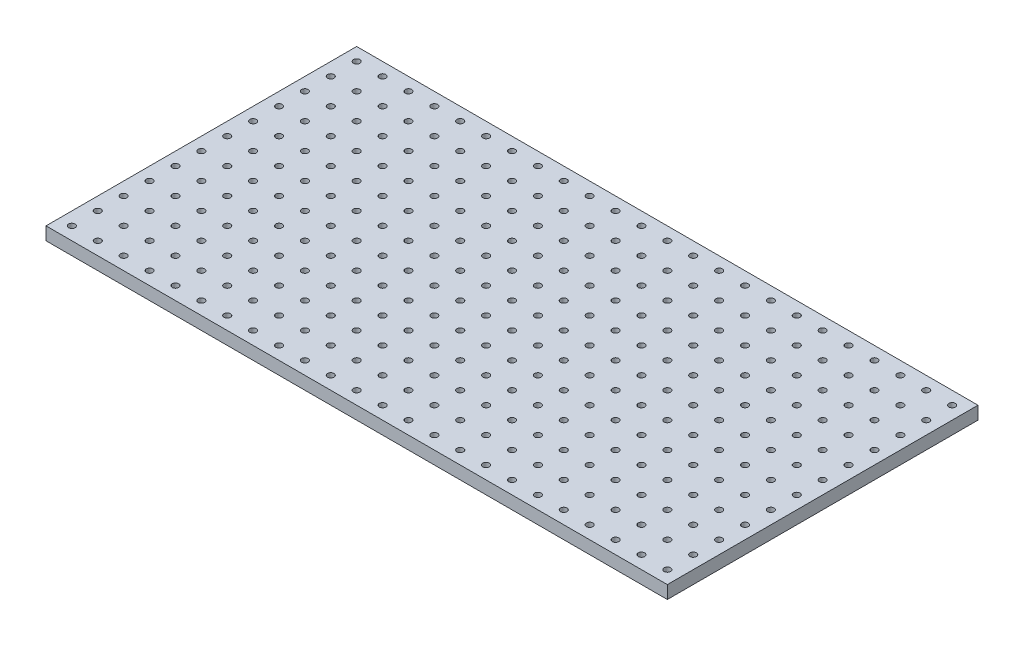
SolidWorks part; units mm, degrees
ref_plane "Front Plane" through (0, 0, 0) normal (0, 0, 1) x (1, 0, 0)
ref_plane "Top Plane" through (0, 0, 0) normal (0, 1, 0) x (1, 0, 0)
ref_plane "Right Plane" through (0, 0, 0) normal (1, 0, 0) x (0, 0, -1)
sketch "Sketch1" plane through (0, 0, 0) normal (0, 1, 0) x (1, 0, 0)
  line L1 (0, 0) -> (609.6, 0)
  line L2 (0, 0) -> (0, 304.8)
  line L3 (0, 304.8) -> (609.6, 304.8)
  line L4 (609.6, 0) -> (609.6, 304.8)
  dimension "D1" = 304.8
  dimension "D2" = 609.6
extrude "Boss-Extrude1" add sketch "Sketch1" along normal blind 12.7
sketch "Sketch2" plane through (0, 12.7, 0) normal (0, 1, 0) x (1, 0, 0)
  line L0 (0, 0) -> (609.6, 0) construction
  line L1 (0, 304.8) -> (0, 0) construction
  circle A0 centre (12.7, 12.7) radius 3.175
  circle A1 centre (38.1, 12.7) radius 3.175
  circle A2 centre (63.5, 12.7) radius 3.175
  circle A3 centre (88.9, 12.7) radius 3.175
  circle A4 centre (114.3, 12.7) radius 3.175
  circle A5 centre (139.7, 12.7) radius 3.175
  circle A6 centre (165.1, 12.7) radius 3.175
  circle A7 centre (190.5, 12.7) radius 3.175
  circle A8 centre (215.9, 12.7) radius 3.175
  circle A9 centre (241.3, 12.7) radius 3.175
  circle A10 centre (266.7, 12.7) radius 3.175
  circle A11 centre (292.1, 12.7) radius 3.175
  circle A12 centre (317.5, 12.7) radius 3.175
  circle A13 centre (342.9, 12.7) radius 3.175
  circle A14 centre (368.3, 12.7) radius 3.175
  circle A15 centre (393.7, 12.7) radius 3.175
  circle A16 centre (419.1, 12.7) radius 3.175
  circle A17 centre (444.5, 12.7) radius 3.175
  circle A18 centre (469.9, 12.7) radius 3.175
  circle A19 centre (495.3, 12.7) radius 3.175
  circle A20 centre (520.7, 12.7) radius 3.175
  circle A21 centre (546.1, 12.7) radius 3.175
  circle A22 centre (571.5, 12.7) radius 3.175
  circle A23 centre (596.9, 12.7) radius 3.175
  circle A24 centre (38.1, 38.1) radius 3.175
  circle A25 centre (63.5, 38.1) radius 3.175
  circle A26 centre (88.9, 38.1) radius 3.175
  circle A27 centre (114.3, 38.1) radius 3.175
  circle A28 centre (139.7, 38.1) radius 3.175
  circle A29 centre (165.1, 38.1) radius 3.175
  circle A30 centre (190.5, 38.1) radius 3.175
  circle A31 centre (215.9, 38.1) radius 3.175
  circle A32 centre (241.3, 38.1) radius 3.175
  circle A33 centre (266.7, 38.1) radius 3.175
  circle A34 centre (292.1, 38.1) radius 3.175
  circle A35 centre (317.5, 38.1) radius 3.175
  circle A36 centre (342.9, 38.1) radius 3.175
  circle A37 centre (368.3, 38.1) radius 3.175
  circle A38 centre (393.7, 38.1) radius 3.175
  circle A39 centre (419.1, 38.1) radius 3.175
  circle A40 centre (444.5, 38.1) radius 3.175
  circle A41 centre (469.9, 38.1) radius 3.175
  circle A42 centre (495.3, 38.1) radius 3.175
  circle A43 centre (520.7, 38.1) radius 3.175
  circle A44 centre (546.1, 38.1) radius 3.175
  circle A45 centre (571.5, 38.1) radius 3.175
  circle A46 centre (596.9, 38.1) radius 3.175
  circle A47 centre (38.1, 63.5) radius 3.175
  circle A48 centre (63.5, 63.5) radius 3.175
  circle A49 centre (88.9, 63.5) radius 3.175
  circle A50 centre (114.3, 63.5) radius 3.175
  circle A51 centre (139.7, 63.5) radius 3.175
  circle A52 centre (165.1, 63.5) radius 3.175
  circle A53 centre (190.5, 63.5) radius 3.175
  circle A54 centre (215.9, 63.5) radius 3.175
  circle A55 centre (241.3, 63.5) radius 3.175
  circle A56 centre (266.7, 63.5) radius 3.175
  circle A57 centre (292.1, 63.5) radius 3.175
  circle A58 centre (317.5, 63.5) radius 3.175
  circle A59 centre (342.9, 63.5) radius 3.175
  circle A60 centre (368.3, 63.5) radius 3.175
  circle A61 centre (393.7, 63.5) radius 3.175
  circle A62 centre (419.1, 63.5) radius 3.175
  circle A63 centre (444.5, 63.5) radius 3.175
  circle A64 centre (469.9, 63.5) radius 3.175
  circle A65 centre (495.3, 63.5) radius 3.175
  circle A66 centre (520.7, 63.5) radius 3.175
  circle A67 centre (546.1, 63.5) radius 3.175
  circle A68 centre (571.5, 63.5) radius 3.175
  circle A69 centre (596.9, 63.5) radius 3.175
  circle A70 centre (38.1, 88.9) radius 3.175
  circle A71 centre (63.5, 88.9) radius 3.175
  circle A72 centre (88.9, 88.9) radius 3.175
  circle A73 centre (114.3, 88.9) radius 3.175
  circle A74 centre (139.7, 88.9) radius 3.175
  circle A75 centre (165.1, 88.9) radius 3.175
  circle A76 centre (190.5, 88.9) radius 3.175
  circle A77 centre (215.9, 88.9) radius 3.175
  circle A78 centre (241.3, 88.9) radius 3.175
  circle A79 centre (266.7, 88.9) radius 3.175
  circle A80 centre (292.1, 88.9) radius 3.175
  circle A81 centre (317.5, 88.9) radius 3.175
  circle A82 centre (342.9, 88.9) radius 3.175
  circle A83 centre (368.3, 88.9) radius 3.175
  circle A84 centre (393.7, 88.9) radius 3.175
  circle A85 centre (419.1, 88.9) radius 3.175
  circle A86 centre (444.5, 88.9) radius 3.175
  circle A87 centre (469.9, 88.9) radius 3.175
  circle A88 centre (495.3, 88.9) radius 3.175
  circle A89 centre (520.7, 88.9) radius 3.175
  circle A90 centre (546.1, 88.9) radius 3.175
  circle A91 centre (571.5, 88.9) radius 3.175
  circle A92 centre (596.9, 88.9) radius 3.175
  circle A93 centre (38.1, 114.3) radius 3.175
  circle A94 centre (63.5, 114.3) radius 3.175
  circle A95 centre (88.9, 114.3) radius 3.175
  circle A96 centre (114.3, 114.3) radius 3.175
  circle A97 centre (139.7, 114.3) radius 3.175
  circle A98 centre (165.1, 114.3) radius 3.175
  circle A99 centre (190.5, 114.3) radius 3.175
  circle A100 centre (215.9, 114.3) radius 3.175
  circle A101 centre (241.3, 114.3) radius 3.175
  circle A102 centre (266.7, 114.3) radius 3.175
  circle A103 centre (292.1, 114.3) radius 3.175
  circle A104 centre (317.5, 114.3) radius 3.175
  circle A105 centre (342.9, 114.3) radius 3.175
  circle A106 centre (368.3, 114.3) radius 3.175
  circle A107 centre (393.7, 114.3) radius 3.175
  circle A108 centre (419.1, 114.3) radius 3.175
  circle A109 centre (444.5, 114.3) radius 3.175
  circle A110 centre (469.9, 114.3) radius 3.175
  circle A111 centre (495.3, 114.3) radius 3.175
  circle A112 centre (520.7, 114.3) radius 3.175
  circle A113 centre (546.1, 114.3) radius 3.175
  circle A114 centre (571.5, 114.3) radius 3.175
  circle A115 centre (596.9, 114.3) radius 3.175
  circle A116 centre (38.1, 139.7) radius 3.175
  circle A117 centre (63.5, 139.7) radius 3.175
  circle A118 centre (88.9, 139.7) radius 3.175
  circle A119 centre (114.3, 139.7) radius 3.175
  circle A120 centre (139.7, 139.7) radius 3.175
  circle A121 centre (165.1, 139.7) radius 3.175
  circle A122 centre (190.5, 139.7) radius 3.175
  circle A123 centre (215.9, 139.7) radius 3.175
  circle A124 centre (241.3, 139.7) radius 3.175
  circle A125 centre (266.7, 139.7) radius 3.175
  circle A126 centre (292.1, 139.7) radius 3.175
  circle A127 centre (317.5, 139.7) radius 3.175
  circle A128 centre (342.9, 139.7) radius 3.175
  circle A129 centre (368.3, 139.7) radius 3.175
  circle A130 centre (393.7, 139.7) radius 3.175
  circle A131 centre (419.1, 139.7) radius 3.175
  circle A132 centre (444.5, 139.7) radius 3.175
  circle A133 centre (469.9, 139.7) radius 3.175
  circle A134 centre (495.3, 139.7) radius 3.175
  circle A135 centre (520.7, 139.7) radius 3.175
  circle A136 centre (546.1, 139.7) radius 3.175
  circle A137 centre (571.5, 139.7) radius 3.175
  circle A138 centre (596.9, 139.7) radius 3.175
  circle A139 centre (38.1, 165.1) radius 3.175
  circle A140 centre (63.5, 165.1) radius 3.175
  circle A141 centre (88.9, 165.1) radius 3.175
  circle A142 centre (114.3, 165.1) radius 3.175
  circle A143 centre (139.7, 165.1) radius 3.175
  circle A144 centre (165.1, 165.1) radius 3.175
  circle A145 centre (190.5, 165.1) radius 3.175
  circle A146 centre (215.9, 165.1) radius 3.175
  circle A147 centre (241.3, 165.1) radius 3.175
  circle A148 centre (266.7, 165.1) radius 3.175
  circle A149 centre (292.1, 165.1) radius 3.175
  circle A150 centre (317.5, 165.1) radius 3.175
  circle A151 centre (342.9, 165.1) radius 3.175
  circle A152 centre (368.3, 165.1) radius 3.175
  circle A153 centre (393.7, 165.1) radius 3.175
  circle A154 centre (419.1, 165.1) radius 3.175
  circle A155 centre (444.5, 165.1) radius 3.175
  circle A156 centre (469.9, 165.1) radius 3.175
  circle A157 centre (495.3, 165.1) radius 3.175
  circle A158 centre (520.7, 165.1) radius 3.175
  circle A159 centre (546.1, 165.1) radius 3.175
  circle A160 centre (571.5, 165.1) radius 3.175
  circle A161 centre (596.9, 165.1) radius 3.175
  circle A162 centre (38.1, 190.5) radius 3.175
  circle A163 centre (63.5, 190.5) radius 3.175
  circle A164 centre (88.9, 190.5) radius 3.175
  circle A165 centre (114.3, 190.5) radius 3.175
  circle A166 centre (139.7, 190.5) radius 3.175
  circle A167 centre (165.1, 190.5) radius 3.175
  circle A168 centre (190.5, 190.5) radius 3.175
  circle A169 centre (215.9, 190.5) radius 3.175
  circle A170 centre (241.3, 190.5) radius 3.175
  circle A171 centre (266.7, 190.5) radius 3.175
  circle A172 centre (292.1, 190.5) radius 3.175
  circle A173 centre (317.5, 190.5) radius 3.175
  circle A174 centre (342.9, 190.5) radius 3.175
  circle A175 centre (368.3, 190.5) radius 3.175
  circle A176 centre (393.7, 190.5) radius 3.175
  circle A177 centre (419.1, 190.5) radius 3.175
  circle A178 centre (444.5, 190.5) radius 3.175
  circle A179 centre (469.9, 190.5) radius 3.175
  circle A180 centre (495.3, 190.5) radius 3.175
  circle A181 centre (520.7, 190.5) radius 3.175
  circle A182 centre (546.1, 190.5) radius 3.175
  circle A183 centre (571.5, 190.5) radius 3.175
  circle A184 centre (596.9, 190.5) radius 3.175
  circle A185 centre (38.1, 215.9) radius 3.175
  circle A186 centre (63.5, 215.9) radius 3.175
  circle A187 centre (88.9, 215.9) radius 3.175
  circle A188 centre (114.3, 215.9) radius 3.175
  circle A189 centre (139.7, 215.9) radius 3.175
  circle A190 centre (165.1, 215.9) radius 3.175
  circle A191 centre (190.5, 215.9) radius 3.175
  circle A192 centre (215.9, 215.9) radius 3.175
  circle A193 centre (241.3, 215.9) radius 3.175
  circle A194 centre (266.7, 215.9) radius 3.175
  circle A195 centre (292.1, 215.9) radius 3.175
  circle A196 centre (317.5, 215.9) radius 3.175
  circle A197 centre (342.9, 215.9) radius 3.175
  circle A198 centre (368.3, 215.9) radius 3.175
  circle A199 centre (393.7, 215.9) radius 3.175
  circle A200 centre (419.1, 215.9) radius 3.175
  circle A201 centre (444.5, 215.9) radius 3.175
  circle A202 centre (469.9, 215.9) radius 3.175
  circle A203 centre (495.3, 215.9) radius 3.175
  circle A204 centre (520.7, 215.9) radius 3.175
  circle A205 centre (546.1, 215.9) radius 3.175
  circle A206 centre (571.5, 215.9) radius 3.175
  circle A207 centre (596.9, 215.9) radius 3.175
  circle A208 centre (38.1, 241.3) radius 3.175
  circle A209 centre (63.5, 241.3) radius 3.175
  circle A210 centre (88.9, 241.3) radius 3.175
  circle A211 centre (114.3, 241.3) radius 3.175
  circle A212 centre (139.7, 241.3) radius 3.175
  circle A213 centre (165.1, 241.3) radius 3.175
  circle A214 centre (190.5, 241.3) radius 3.175
  circle A215 centre (215.9, 241.3) radius 3.175
  circle A216 centre (241.3, 241.3) radius 3.175
  circle A217 centre (266.7, 241.3) radius 3.175
  circle A218 centre (292.1, 241.3) radius 3.175
  circle A219 centre (317.5, 241.3) radius 3.175
  circle A220 centre (342.9, 241.3) radius 3.175
  circle A221 centre (368.3, 241.3) radius 3.175
  circle A222 centre (393.7, 241.3) radius 3.175
  circle A223 centre (419.1, 241.3) radius 3.175
  circle A224 centre (444.5, 241.3) radius 3.175
  circle A225 centre (469.9, 241.3) radius 3.175
  circle A226 centre (495.3, 241.3) radius 3.175
  circle A227 centre (520.7, 241.3) radius 3.175
  circle A228 centre (546.1, 241.3) radius 3.175
  circle A229 centre (571.5, 241.3) radius 3.175
  circle A230 centre (596.9, 241.3) radius 3.175
  circle A231 centre (38.1, 266.7) radius 3.175
  circle A232 centre (63.5, 266.7) radius 3.175
  circle A233 centre (88.9, 266.7) radius 3.175
  circle A234 centre (114.3, 266.7) radius 3.175
  circle A235 centre (139.7, 266.7) radius 3.175
  circle A236 centre (165.1, 266.7) radius 3.175
  circle A237 centre (190.5, 266.7) radius 3.175
  circle A238 centre (215.9, 266.7) radius 3.175
  circle A239 centre (241.3, 266.7) radius 3.175
  circle A240 centre (266.7, 266.7) radius 3.175
  circle A241 centre (292.1, 266.7) radius 3.175
  circle A242 centre (317.5, 266.7) radius 3.175
  circle A243 centre (342.9, 266.7) radius 3.175
  circle A244 centre (368.3, 266.7) radius 3.175
  circle A245 centre (393.7, 266.7) radius 3.175
  circle A246 centre (419.1, 266.7) radius 3.175
  circle A247 centre (444.5, 266.7) radius 3.175
  circle A248 centre (469.9, 266.7) radius 3.175
  circle A249 centre (495.3, 266.7) radius 3.175
  circle A250 centre (520.7, 266.7) radius 3.175
  circle A251 centre (546.1, 266.7) radius 3.175
  circle A252 centre (571.5, 266.7) radius 3.175
  circle A253 centre (596.9, 266.7) radius 3.175
  circle A254 centre (38.1, 292.1) radius 3.175
  circle A255 centre (63.5, 292.1) radius 3.175
  circle A256 centre (88.9, 292.1) radius 3.175
  circle A257 centre (114.3, 292.1) radius 3.175
  circle A258 centre (139.7, 292.1) radius 3.175
  circle A259 centre (165.1, 292.1) radius 3.175
  circle A260 centre (190.5, 292.1) radius 3.175
  circle A261 centre (215.9, 292.1) radius 3.175
  circle A262 centre (241.3, 292.1) radius 3.175
  circle A263 centre (266.7, 292.1) radius 3.175
  circle A264 centre (292.1, 292.1) radius 3.175
  circle A265 centre (317.5, 292.1) radius 3.175
  circle A266 centre (342.9, 292.1) radius 3.175
  circle A267 centre (368.3, 292.1) radius 3.175
  circle A268 centre (393.7, 292.1) radius 3.175
  circle A269 centre (419.1, 292.1) radius 3.175
  circle A270 centre (444.5, 292.1) radius 3.175
  circle A271 centre (469.9, 292.1) radius 3.175
  circle A272 centre (495.3, 292.1) radius 3.175
  circle A273 centre (520.7, 292.1) radius 3.175
  circle A274 centre (546.1, 292.1) radius 3.175
  circle A275 centre (571.5, 292.1) radius 3.175
  circle A276 centre (596.9, 292.1) radius 3.175
  circle A277 centre (12.7, 38.1) radius 3.175
  circle A278 centre (12.7, 63.5) radius 3.175
  circle A279 centre (12.7, 88.9) radius 3.175
  circle A280 centre (12.7, 114.3) radius 3.175
  circle A281 centre (12.7, 139.7) radius 3.175
  circle A282 centre (12.7, 165.1) radius 3.175
  circle A283 centre (12.7, 190.5) radius 3.175
  circle A284 centre (12.7, 215.9) radius 3.175
  circle A285 centre (12.7, 241.3) radius 3.175
  circle A286 centre (12.7, 266.7) radius 3.175
  circle A287 centre (12.7, 292.1) radius 3.175
  dimension "D1" = 6.35
  dimension "D2" = 12.7
  dimension "D3" = 12.7
  dimension "D4" = 24
  dimension "D5" = 12
extrude "Cut-Extrude1" cut sketch "Sketch2" against normal through all
